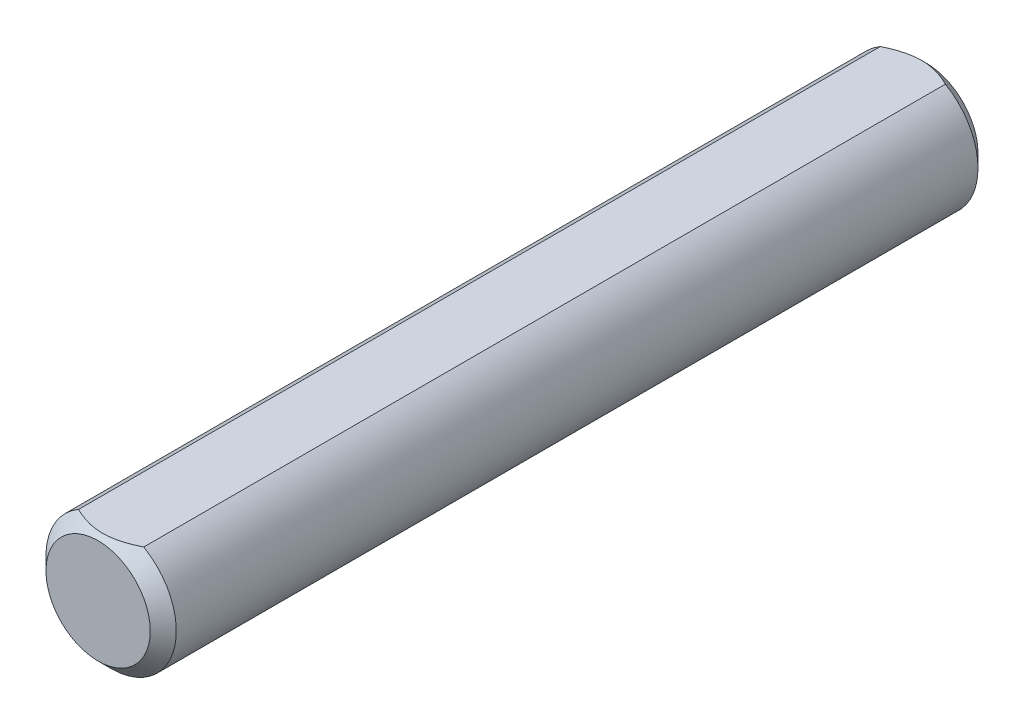
SolidWorks part; units mm, degrees
ref_plane "Front" through (0, 0, 0) normal (0, 0, 1) x (1, 0, 0)
ref_plane "Top" through (0, 0, 0) normal (0, 1, 0) x (1, 0, 0)
ref_plane "Right" through (0, 0, 0) normal (1, 0, 0) x (0, 0, -1)
sketch "Sketch1" plane through (0, 0, 0) normal (0, 0, 1) x (1, 0, 0)
  circle A0 centre (0, 0) radius 3
  dimension "D1" = 6
extrude "Extrude1" add sketch "Sketch1" along normal mid plane 38.1
chamfer "Chamfer1" distance 0.6 angle 45 2 edges at (3, 0, -19.05) (3, 0, 19.05)
sketch "Sketch13" plane through (0, 0, 0) normal (0, 0, 1) x (1, 0, 0)
  line L3 (-1.5, 2.5981) -> (1.5, 2.5981)
  circle A0 centre (0, 0) radius 3 construction
  arc A1 (1.5, 2.5981) -> (-1.5, 2.5981) centre (0, 0) ccw
  dimension "D1" = 3
extrude "Extrude7" cut sketch "Sketch13" against normal through all and the other way through all
equation "\"D1@Chamfer1\" = \"D1@Sketch1\" * .1"
equation "\"D1@Sketch13\" = \"D1@Sketch1\" * .5"
